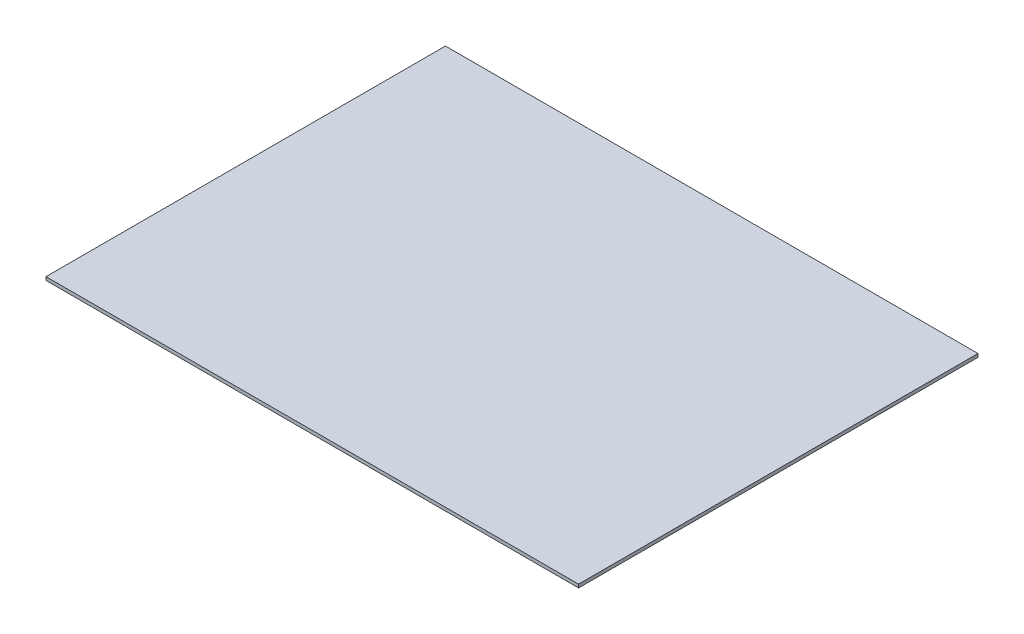
SolidWorks part; units mm, degrees
material "Maple"
ref_plane "Front Plane" through (0, 0, 0) normal (0, 0, 1) x (1, 0, 0)
ref_plane "Top Plane" through (0, 0, 0) normal (0, 1, 0) x (1, 0, 0)
ref_plane "Right Plane" through (0, 0, 0) normal (1, 0, 0) x (0, 0, -1)
sketch "Sketch1" plane through (0, 0, 0) normal (0, 1, 0) x (1, 0, 0)
  line L2 (-400, 300) -> (400, 300)
  line L3 (400, 300) -> (400, -300)
  line L4 (400, -300) -> (-400, -300)
  line L5 (-400, -300) -> (-400, 300)
extrude "Boss-Extrude1" add sketch "Sketch1" along normal blind 5 contours L5 L2 L3 L4
